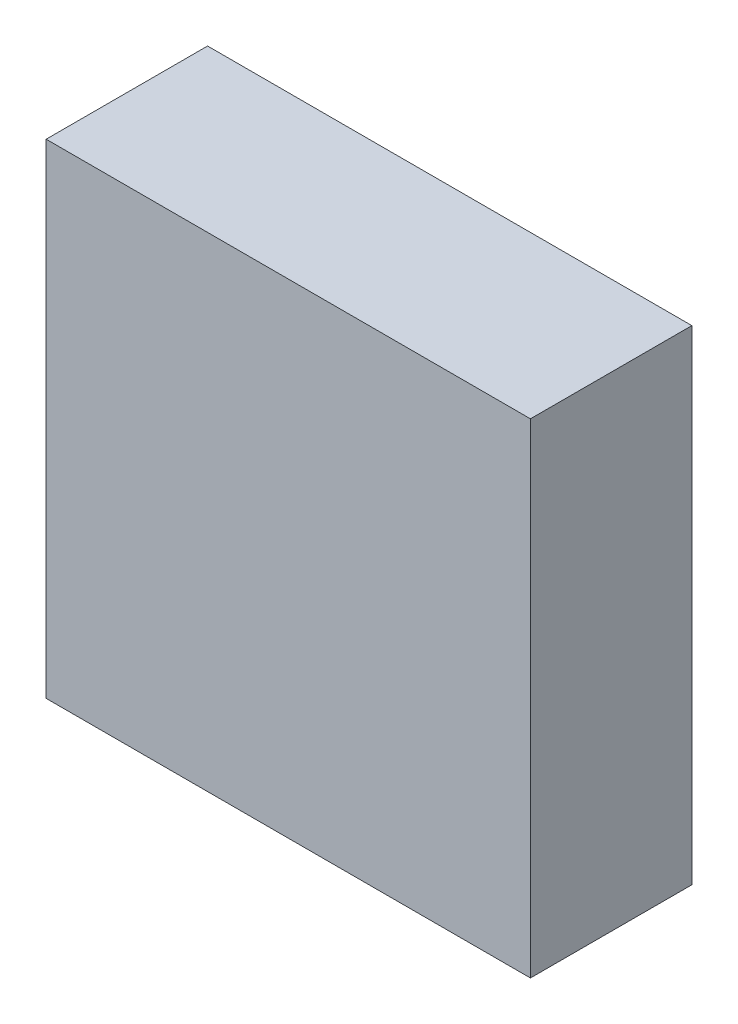
SolidWorks part; units mm, degrees
ref_plane "Plan de face" through (0, 0, 0) normal (0, 0, 1) x (1, 0, 0)
ref_plane "Plan de dessus" through (0, 0, 0) normal (0, 1, 0) x (1, 0, 0)
ref_plane "Plan de droite" through (0, 0, 0) normal (1, 0, 0) x (0, 0, -1)
sketch "Esquisse1" plane through (0, 0, 0) normal (0, 0, 1) x (1, 0, 0)
  line L1 (0, 0) -> (3, 0)
  line L2 (0, 0) -> (0, 3)
  line L3 (0, 3) -> (3, 3)
  line L4 (3, 0) -> (3, 3)
extrude "Boss.-Extru.1" add sketch "Esquisse1" along normal blind 1
